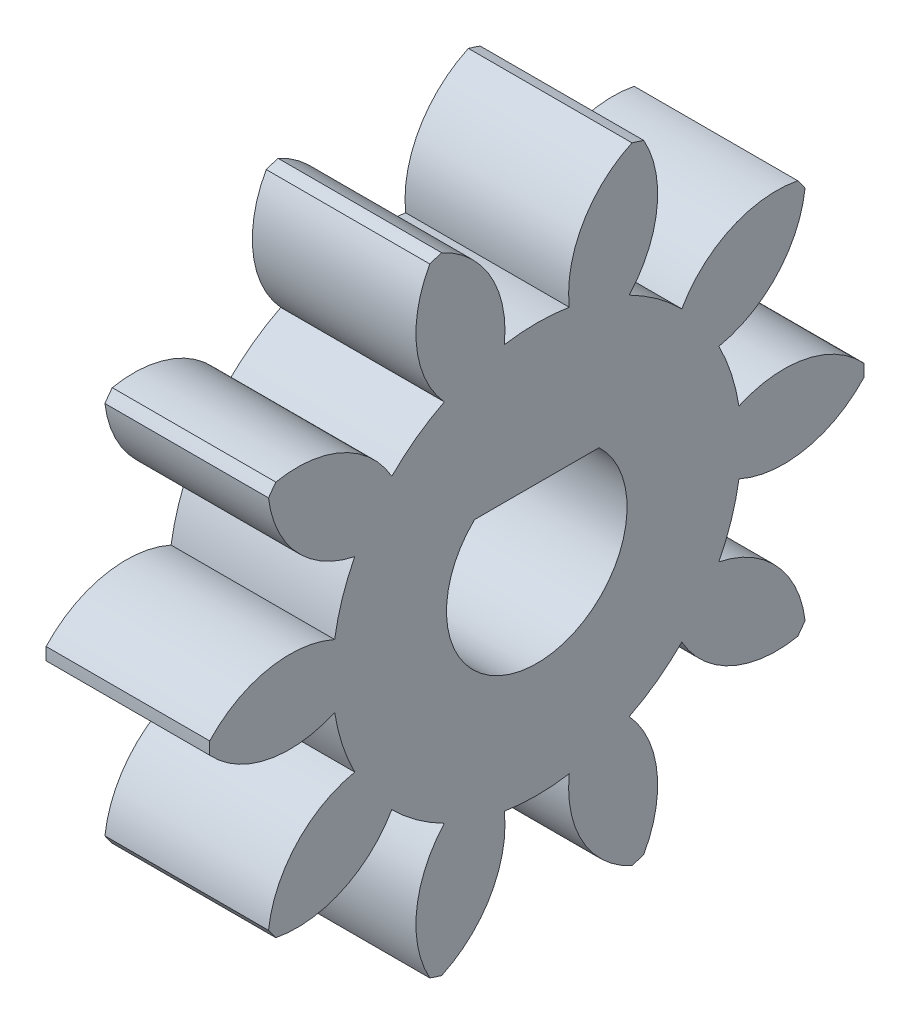
SolidWorks part; units mm, degrees
ref_plane "Plane1" through (0, 0, 0) normal (0, 0, 1) x (1, 0, 0)
ref_plane "Plane2" through (0, 0, 0) normal (0, 1, 0) x (1, 0, 0)
ref_plane "Plane3" through (0, 0, 0) normal (1, 0, 0) x (0, 0, -1)
sketch "HoldingSke" plane through (0, 0, 0) normal (0, 1, 0) x (1, 0, 0)
  line L0 (0, 0) -> (600.3388, -105.8559)
  line L1 (-15, 0) -> (100, 0) construction
  line L2 (0, 0) -> (-2.1039, 2.3779)
  line L3 (0, 0) -> (-11.863, 4.5341)
  line L4 (0, 0) -> (8.5048, 1.4996)
  line L5 (0, 0) -> (-47.5972, -17.7524)
  line L6 (0, 0) -> (-2.632, -1.7758)
  line L7 (-2.1039, 2.3779) -> (8.8308, 51.9871)
  line L8 (-76.2, 54.61) -> (-74.168, 54.61)
  line L9 (-71.009, 38.7566) -> (-53.1078, 45.2721)
  line L10 (-76.2, 71.12) -> (104.1128, 71.12)
  line L11 (0, 0) -> (-3.175, 0)
  line L12 (-76.2, 101.6) -> (-76.1573, 101.6)
  line L13 (24.9733, 27.94) -> (52.9518, 28.4284)
  line L14 (24.9733, 27.94) -> (25.0241, 27.9398)
  line L15 (24.9733, 27.94) -> (100.4021, 29.52)
  circle A0 centre (0, 0) radius 0.9995
  circle A1 centre (0, 0) radius 3.9709
  circle A2 centre (0, 0) radius 38.1
  circle A3 centre (0, 0) radius 0.9995
  dimension "MHD" = 7.9417
  dimension "Hub_dia" = 76.2
  dimension "Bore" = 1.999
  dimension "MBD" = 1.999
  dimension "Num_teeth" = 10
  dimension "Pitch" = 609.6
  dimension "Overall_len" = 50.8
  dimension "Show_teeth" = 10
  dimension "Thickness" = 3.175
  dimension "OAL" = 50.8001
  dimension "T_dim" = 2.032
  dimension "Ap" = 20
  dimension "H" = 19.05
  dimension "Pitch_radius" = 180.3128
  dimension "Width" = 3.175
  dimension "Backlash" = 0.0427
  dimension "Addendum_fac" = 1
  dimension "Dedendum_fac" = 1.2
  dimension "Clearance_fac" = 0.2
  dimension "Dedendum_add" = 0.0508
sketch "BasProSke" plane through (0, 0, 0) normal (0, 1, 0) x (1, 0, 0)
  line L0 (-10, 0) -> (60, 0) construction
  line L1 (0, 0) -> (0, 6.35)
  line L2 (0, 0) -> (3.175, 0)
  line L3 (3.175, 0) -> (3.175, 6.35)
  line L4 (3.175, 6.35) -> (0, 6.35)
  dimension "Thickness" = 3.175
  dimension "Diameter" = 12.7
revolve "Base-Revolve" add sketch "BasProSke" angle 360 about L0
sketch "TooCutSke" plane through (0, 0, 0) normal (1, 0, 0) x (0, 0, -1)
  line L1 (0, 0) -> (0, 107) construction
  line L2 (0, 0) -> (-0.9023, 5.2142) construction
  line L3 (0, 0) -> (-3.2371, 9.9629) construction
  line L4 (-0.9023, 5.2142) -> (-1.6186, 4.9814) construction
  arc A0 (0.6302, 3.9205) -> (-0.6302, 3.9205) centre (0, 0) ccw
  arc A1 (1.8823, 6.0912) -> (-1.8823, 6.0912) centre (0, 0) ccw
  circle A2 centre (0, 0) radius 5.2917 construction
  circle A3 centre (0, 0) radius 4.9725 construction
  arc A4 (-0.6302, 3.9205) -> (-1.8823, 6.0912) centre (-2.734, 4.1535) ccw
  arc A5 (1.8823, 6.0912) -> (0.6302, 3.9205) centre (2.734, 4.1535) ccw
  dimension "Root_dia" = 7.9417
  dimension "Overcut_dia" = 12.7508
  dimension "Pitch_dia" = 10.5833
  dimension "Base_dia" = 9.9451
  dimension "Flank_rad" = 2.1167
  dimension "Half_ang" = 18
  dimension "Half_CT" = 0.7531
extrude "ToothCut" cut sketch "TooCutSke" along normal through all
fillet "Breaks" [suppressed] radius 0.0212
fillet "RootFillets" [suppressed] radius 0.2625
pattern_circular "TeethCuts" count 10 every 36 about axis through (-10, 0, 0) along (1, 0, 0) of "ToothCut", "RootFillets", "Breaks"
sketch "HubNeaOneSke" plane through (0, 0, 0) normal (-1, 0, 0) x (0, 0, 1)
  circle A0 centre (0, 0) radius 3.9709
  dimension "Diameter" = 7.9417
extrude "HubNearOne" [suppressed] add sketch "HubNeaOneSke" along normal blind 47.6251
sketch "HubNeaBotSke" plane through (0, 0, 0) normal (-1, 0, 0) x (0, 0, 1)
  circle A0 centre (0, 0) radius 3.9709
  dimension "Diameter" = 7.9417
extrude "HubNearBoth" [suppressed] add sketch "HubNeaBotSke" along normal blind 23.8125
ref_plane "FarPln" through (3.175, 0, 0) normal (1, 0, 0) x (0, 0, -1)
sketch "HubFarSke" plane through (3.175, 0, 0) normal (1, 0, 0) x (0, 0, -1)
  circle A0 centre (0, 0) radius 3.9709
  dimension "Diameter" = 7.9417
extrude "HubFar" [suppressed] add sketch "HubFarSke" along normal blind 23.8125
sketch "BorSke" plane through (0, 0, 0) normal (1, 0, 0) x (0, 0, -1)
  circle A0 centre (0, 0) radius 0.9995
  dimension "Diameter" = 1.999
extrude "Bore" cut sketch "BorSke" along normal mid plane 101.6001
sketch "KeySke" plane through (0, 0, 0) normal (1, 0, 0) x (0, 0, -1)
  line L0 (-0.127, 0) -> (-0.127, 1.0325)
  line L1 (-0.127, 1.0325) -> (0.127, 1.0325)
  line L2 (0.127, 1.0325) -> (0.127, 0)
  line L3 (0, 0) -> (0, 34) construction
  line L4 (-0.127, 0) -> (0.127, 0)
  dimension "Offset" = 1.0325
  dimension "Width" = 0.254
extrude "Keyway" [suppressed] cut sketch "KeySke" along normal mid plane 101.6001
pattern_circular "Keyway2" [suppressed] count 2 every 90 about axis through (-10, 0, 0) along (1, 0, 0)
sketch "Sketch1" plane through (3.175, 0, 0) normal (1, 0, 0) x (0, 0, -1)
  line L0 (-1.1016, 1.016) -> (1.1016, 1.016) construction
  line L1 (-2.2991, -1.4986) -> (2.7261, -1.4986) construction
  line L2 (-1.2078, 1.27) -> (1.2078, 1.27)
  arc A0 (-1.1016, 1.016) -> (1.1016, 1.016) centre (0, 0) ccw construction
  arc A1 (-1.2078, 1.27) -> (1.2078, 1.27) centre (0, 0) ccw
  dimension "D1" = 2.9972
  dimension "D2" = 2.5146
  dimension "D3" = 0.254
extrude "Cut-Extrude1" cut sketch "Sketch1" against normal through all
equation "' \"Pitch@HoldingSke\" = 4"
equation "' \"Num_teeth@HoldingSke\" = 12"
equation "' \"Ap@HoldingSke\" =  20"
equation "' \"Ap@HoldingSke\" = 20"
equation "' \"Width@HoldingSke\" = 0.5"
equation "' \"Hub_dia@HoldingSke\"= 1"
equation "' \"Hub_dia@HoldingSke\" = 1"
equation "' \"Overall_len@HoldingSke\" = 1.0"
equation "' \"Bore@HoldingSke\" = 0.75"
equation "' \"T_dim@HoldingSke\" = 0.85"
equation "' \"Width@KeySke\" = 0.25"
equation "' \"Show_teeth@HoldingSke\" = 13"
equation "' \"Backlash@HoldingSke\" = 0.009"
equation "' \"Addendum_fac@HoldingSke\" = 1.0"
equation "' \"Dedendum_fac@HoldingSke\" = 1.25"
equation "' \"Dedendum_add@HoldingSke\" = 0.00005"
equation "' \"Clearance_fac@HoldingSke\" = 0.25"
equation "' \"Pitch@HoldingSke\" = 0.5"
equation "' \"Num_teeth@HoldingSke\" = 23"
equation "' \"Show_teeth@HoldingSke\" = 23"
equation "' \"Backlash@HoldingSke\" = 0.0375"
equation "\"Overcut_dia@TooCutSke\" = (\"Num_teeth@HoldingSke\" + 2 * \"Addendum_fac@HoldingSke\") / \"Pitch@HoldingSke\" + 0.002"
equation "\"Pitch_dia@TooCutSke\" = \"Num_teeth@HoldingSke\" / \"Pitch@HoldingSke\""
equation "\"Base_dia@TooCutSke\" = \"Num_teeth@HoldingSke\" / \"Pitch@HoldingSke\" * cos((\"Ap@HoldingSke\"  * 3.14159265 / 180))"
equation "\"Root_dia@TooCutSke\" = (\"Num_teeth@HoldingSke\" + 2) / \"Pitch@HoldingSke\" - 2 * (\"Addendum_fac@HoldingSke\" + \"Dedendum_fac@HoldingSke\") / \"Pitch@HoldingSke\" - \"Dedendum_add@HoldingSke\" * 2"
equation "\"Half_ang@TooCutSke\" = 180 / \"Num_teeth@HoldingSke\""
equation "\"Half_CT@TooCutSke\" = \"Num_teeth@HoldingSke\" / \"Pitch@HoldingSke\" * sin((3.14159265 / 2 / \"Num_teeth@HoldingSke\")) / 2 - 7 * \"Backlash@HoldingSke\" / 4"
equation "\"Flank_rad@TooCutSke\" = \"Num_teeth@HoldingSke\" / \"Pitch@HoldingSke\" / 5"
equation "\"Radius@RootFillets\" = \"Clearance_fac@HoldingSke\" / \"Pitch@HoldingSke\" + \"Dedendum_add@HoldingSke\""
equation "\"Break_rad@Breaks\" = 0.02 / \"Pitch@HoldingSke\""
equation "\"Thickness@HoldingSke\" = \"Width@HoldingSke\""
equation "\"OAL@HoldingSke\" = \"Thickness@HoldingSke\""
equation "\"MHD@HoldingSke\" = (\"Num_teeth@HoldingSke\" + 2) / \"Pitch@HoldingSke\" - 2 * (\"Addendum_fac@HoldingSke\" + \"Dedendum_fac@HoldingSke\")  / \"Pitch@HoldingSke\" - \"Dedendum_add@HoldingSke\" * 2"
equation "\"MBD@HoldingSke\" = (\"Num_teeth@HoldingSke\" + 2) / \"Pitch@HoldingSke\" - 2 * (\"Addendum_fac@HoldingSke\" + \"Dedendum_fac@HoldingSke\")  / \"Pitch@HoldingSke\" - \"Dedendum_add@HoldingSke\" * 2 - 0.002"
equation "\"MHD@HoldingSke\" = ((sgn( \"MHD@HoldingSke\" - \"Hub_dia@HoldingSke\" )-1)*( \"MHD@HoldingSke\" - \"Hub_dia@HoldingSke\" ))/-2+ \"Hub_dia@HoldingSke\""
equation "\"MBD@HoldingSke\" = ((sgn( \"MBD@HoldingSke\" - \"Bore@HoldingSke\" )-1)*( \"MBD@HoldingSke\" - \"Bore@HoldingSke\" ))/-2+ \"Bore@HoldingSke\""
equation "\"OAL@HoldingSke\" = ((sgn( \"OAL@HoldingSke\" - \"Overall_len@HoldingSke\" )+1)*( \"OAL@HoldingSke\" - \"Overall_len@HoldingSke\" ))/2 + \"Overall_len@HoldingSke\" + 0.000002"
equation "\"Num_teeth@TeethCuts\" = int( \"Show_teeth@HoldingSke\" ) + 1"
equation "\"Num_teeth@TeethCuts\" = ((sgn( \"Num_teeth@TeethCuts\" - \"Num_teeth@HoldingSke\" )-1)*( \"Num_teeth@TeethCuts\" - \"Num_teeth@HoldingSke\" ))/-2+ \"Num_teeth@HoldingSke\""
equation "\"Num_teeth@TeethCuts\" = ((sgn( \"Num_teeth@TeethCuts\" - 2.0)+1)*( \"Num_teeth@TeethCuts\" - 2.0))/2 +2.0"
equation "\"Angle@TeethCuts\" = 360.0 / \"Num_teeth@HoldingSke\""
equation "\"Diameter@BasProSke\" = (\"Num_teeth@HoldingSke\" + 2 * \"Addendum_fac@HoldingSke\") / \"Pitch@HoldingSke\""
equation "\"Thickness@BasProSke\"  = \"Thickness@HoldingSke\""
equation "' \"Fillet_rad@BasProSke\" =  \"Thickness@HoldingSke\" * 0.05"
equation "' \"Fillet_rad@BasProSke\" = \"Thickness@HoldingSke\" * 0.05"
equation "\"MHD@HoldingSke\" = ((sgn( \"MHD@HoldingSke\" - \"Root_dia@TooCutSke\" )-1)*( \"MHD@HoldingSke\" - \"Root_dia@TooCutSke\" ))/-2+ \"Root_dia@TooCutSke\""
equation "\"Diameter@HubNeaOneSke\" = \"MHD@HoldingSke\""
equation "\"Length@HubNearOne\" = \"OAL@HoldingSke\" - \"Thickness@BasProSke\""
equation "\"Diameter@HubNeaBotSke\" = \"MHD@HoldingSke\""
equation "\"Length@HubNearBoth\" = ( \"OAL@HoldingSke\" - \"Thickness@BasProSke\" ) / 2.0"
equation "\"Thickness@FarPln\" = \"Thickness@BasProSke\""
equation "\"Diameter@HubFarSke\" = \"MHD@HoldingSke\""
equation "\"Length@HubFar\" = ( \"OAL@HoldingSke\" - \"Thickness@BasProSke\" ) / 2.0"
equation "\"Diameter@BorSke\" = \"MBD@HoldingSke\""
equation "\"D1@Bore\" = \"OAL@HoldingSke\" * 2.0"
equation "\"D1@Keyway\" = \"OAL@HoldingSke\" * 2.0"
equation "\"Offset@KeySke\" = \"T_dim@HoldingSke\" - \"MBD@HoldingSke\" / 2.0"
